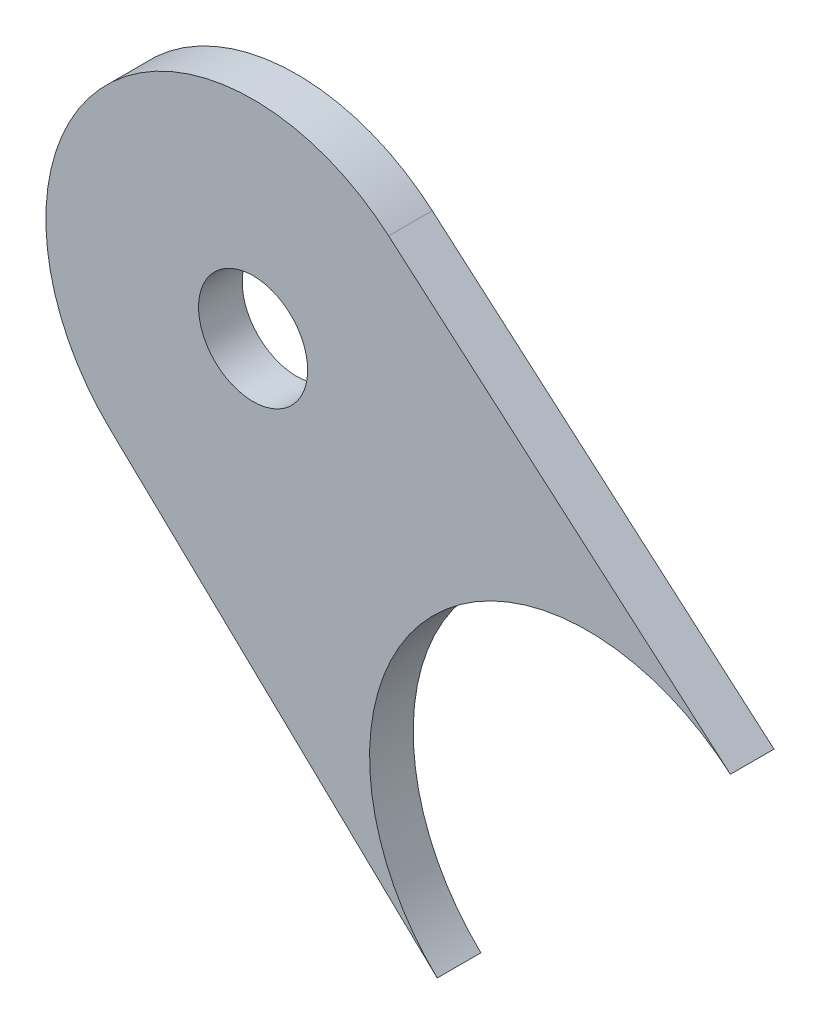
SolidWorks part; units mm, degrees
material "AISI 4130 Steel, normalized at 870C"
ref_plane "Front Plane" through (0, 0, 0) normal (0, 0, 1) x (1, 0, 0)
ref_plane "Top Plane" through (0, 0, 0) normal (0, 1, 0) x (1, 0, 0)
ref_plane "Right Plane" through (0, 0, 0) normal (1, 0, 0) x (0, 0, -1)
sketch "Sketch2" plane through (0, 0, 0) normal (0, 0, 1) x (1, 0, 0)
  line L2 (111.7527, -67.172) -> (131.6483, -84.3726)
  line L3 (95.5401, -85.0345) -> (114.5825, -103.1753)
  circle A2 centre (103.862, -76.299) radius 12.065 construction
  circle A3 centre (123.3424, -93.98) radius 12.7 construction
  arc A5 (95.5401, -85.0345) -> (111.7527, -67.172) centre (103.862, -76.299) cw
  arc A6 (114.5825, -103.1753) -> (131.6483, -84.3726) centre (123.3424, -93.98) cw
  circle A9 centre (103.862, -76.299) radius 3.175
  dimension "D1" = 6.35
extrude "Boss-Extrude3" add sketch "Sketch2" along normal blind 2.54 from offset 4.7625
ref_point "Point2"
